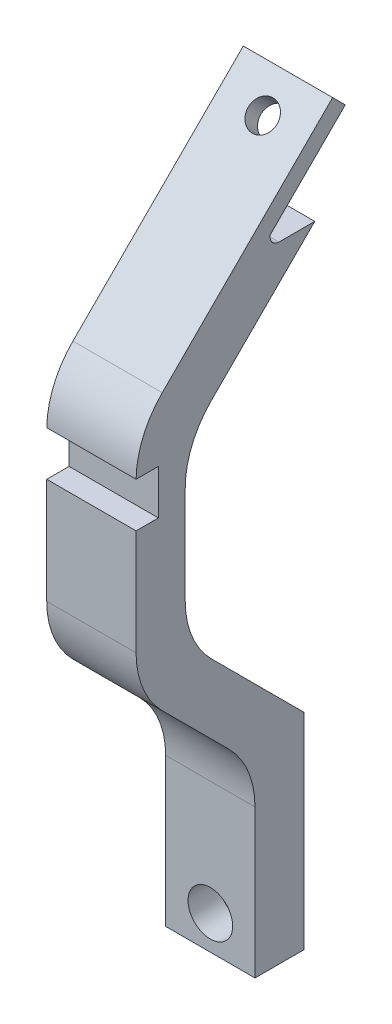
SolidWorks part; units mm, degrees
ref_plane "Piano frontale" through (0, 0, 0) normal (0, 0, 1) x (1, 0, 0)
ref_plane "Piano superiore" through (0, 0, 0) normal (0, 1, 0) x (1, 0, 0)
ref_plane "Piano destro" through (0, 0, 0) normal (1, 0, 0) x (0, 0, -1)
sketch "Schizzo1" plane through (0, 0, 0) normal (1, 0, 0) x (0, 0, -1)
  line L0 (-21.1885, 88.9449) -> (-26.6885, 88.9449)
  line L1 (-26.6885, 88.9449) -> (-26.6885, 109.6667)
  line L2 (-26.6885, 109.6667) -> (-40, 122.9783)
  line L3 (-40, 122.9783) -> (-40, 147.9449)
  line L4 (-40, 147.9449) -> (-18, 169.9449)
  line L6 (-25, 158.9449) -> (-20, 158.9449)
  line L9 (-20, 158.9449) -> (-34.5, 144.4449)
  line L10 (-34.5, 144.4449) -> (-34.5, 125.2564)
  line L11 (-34.5, 125.2564) -> (-21.1885, 111.9449)
  line L12 (-21.1885, 111.9449) -> (-21.1885, 88.9449)
  line L13 (-25, 158.9449) -> (-25, 160.1165)
  line L14 (-21.1885, 89.5249) -> (-21.1885, 111.9449) construction
  line L15 (-25, 158.9449) -> (-25, 162.9449) construction
  line L16 (-25, 160.1165) -> (-16.5858, 168.5307)
  line L17 (-16.5858, 168.5307) -> (-18, 169.9449)
  dimension "D1" = 5.5
  dimension "D2" = 5.5
  dimension "D3" = 5.5
  dimension "D4" = 2
  dimension "D5" = 4
  dimension "D6" = 5
  dimension "D7" = 15
  dimension "D8" = 23
  dimension "D9" = 70
  dimension "D10" = 11
  dimension "D12" = 135
extrude "Estrusione-Estrusione1" add sketch "Schizzo1" along normal mid plane 10
sketch "Schizzo2" plane through (0, 0, 26.6885) normal (0, 0, 1) x (1, 0, 0)
  circle A0 centre (0, 92.7235) radius 1.625
  dimension "D1" = 3.25
extrude "Taglio-Estrusione1" cut sketch "Schizzo2" against normal through all
sketch "Schizzo3" plane through (0, 0, 26.6885) normal (0, 0, 1) x (1, 0, 0)
  circle A0 centre (0, 92.7235) radius 2.5
extrude "Taglio-Estrusione2" cut sketch "Schizzo3" against normal blind 3.5
fillet "Raccordo1" radius 10 5 edges at (0, 147.9449, 40) (0, 144.4449, 34.5) (0, 125.2564, 34.5) (0, 122.9783, 40) (0, 109.6667, 26.6885)
sketch "Schizzo4" plane through (-5, 0, 0) normal (-1, 0, 0) x (0, 0, 1)
  line L0 (40, 143.8028) -> (40, 127.1204) construction
  line L1 (40, 143.9449) -> (37.5, 143.9449)
  line L2 (40, 143.9449) -> (40, 138.9449)
  line L3 (40, 138.9449) -> (37.5, 138.9449)
  line L4 (37.5, 143.9449) -> (37.5, 138.9449)
  line L5 (20, 158.9449) -> (25, 158.9449) construction
  dimension "D1" = 5
  dimension "D2" = 2.5
  dimension "D3" = 15
extrude "Taglio-Estrusione3" cut sketch "Schizzo4" against normal blind 10
fillet "Raccordo2" radius 1 1 edges at (0, 158.9449, 25)
sketch "Schizzo5" plane through (0, 93.9725, 93.9725) normal (0, 0.7071, 0.7071) x (1, 0, 0)
  line L0 (5, 107.4413) -> (-5, 107.4413) construction
  line L1 (5, 107.4413) -> (5, 80.4707) construction
  circle A0 centre (0, 103.4413) radius 1.625
  dimension "D1" = 3.25
  dimension "D2" = 4
  dimension "D3" = 5
extrude "Taglio-Estrusione4" cut sketch "Schizzo5" against normal blind 10
